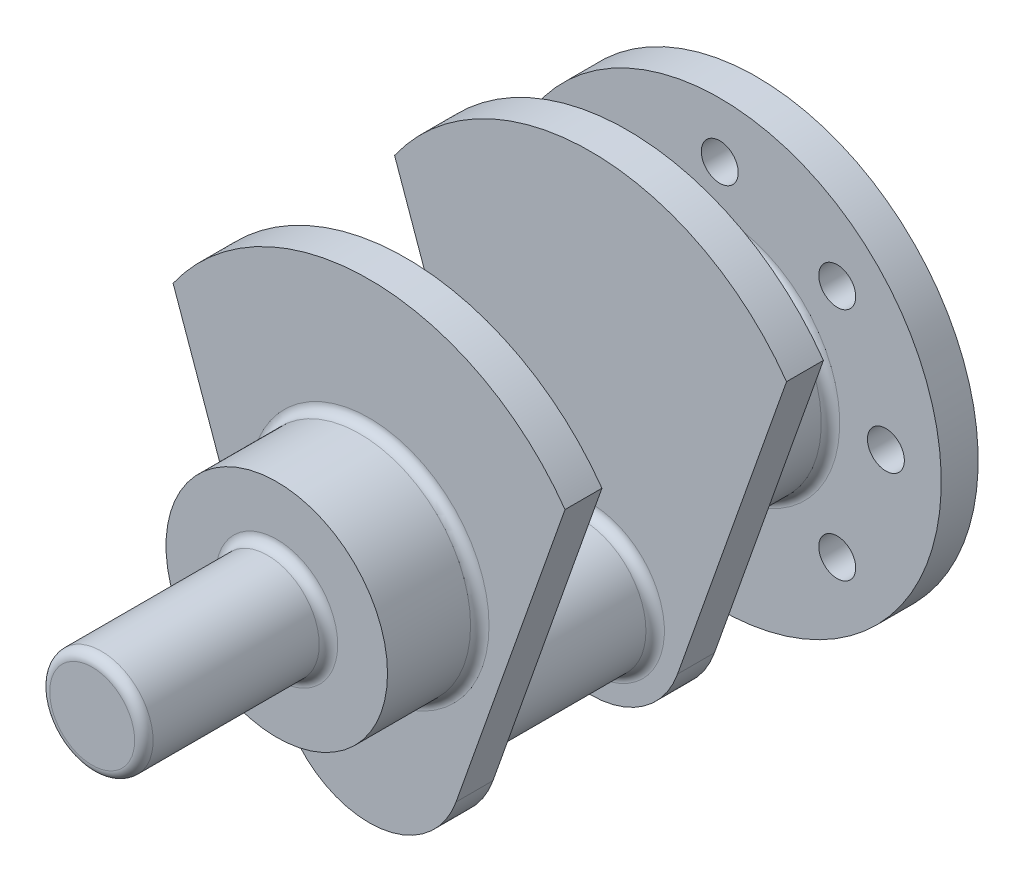
SolidWorks part; units mm, degrees
ref_plane "前视基准面" through (0, 0, 0) normal (0, 0, 1) x (1, 0, 0)
ref_plane "上视基准面" through (0, 0, 0) normal (0, 1, 0) x (1, 0, 0)
ref_plane "右视基准面" through (0, 0, 0) normal (1, 0, 0) x (0, 0, -1)
other "Configuration Table"
sketch "草图1" plane through (0, 0, 0) normal (0, 0, 1) x (1, 0, 0)
  line L0 (0, 60.1764) -> (0, -75) construction
  line L1 (-83.4577, 0) -> (70.0413, 0) construction
  line L2 (-106.1681, 75.0222) -> (-47.1321, -91.6903)
  line L3 (106.1681, 75.0222) -> (47.1321, -91.6903)
  circle A0 centre (0, -75) radius 50
  arc A1 (-106.1681, 75.0222) -> (106.1681, 75.0222) centre (0, 0) cw
  dimension "D1" = 100
  dimension "D3" = 130
  dimension "D2" = 39
  dimension "D4" = 75
extrude "凸台-拉伸1" add sketch "草图1" along normal blind 20 contours A1 L2 A0 L3 | A0
sketch "草图2" plane through (0, 0, 0) normal (0, 0, -1) x (-1, 0, 0)
  circle A0 centre (0, -75) radius 35
extrude "凸台-拉伸2" add sketch "草图2" along normal blind 100
sketch "草图3" plane through (0, 0, 20) normal (0, 0, 1) x (1, 0, 0)
  circle A0 centre (0, 0) radius 60
  dimension "D1" = 120
extrude "凸台-拉伸3" add sketch "草图3" along normal blind 50
ref_plane "基准面1" through (0, 0, -50) normal (0, 0, -1) x (-1, 0, 0)
mirror "镜向1" about plane through (0, 0, -50) normal (0, 0, -1) of "凸台-拉伸1", "凸台-拉伸3"
sketch "草图5" plane through (0, 0, 70) normal (0, 0, 1) x (1, 0, 0)
  circle A0 centre (0, 0) radius 28
extrude "凸台-拉伸4" add sketch "草图5" along normal blind 100
sketch "草图7" plane through (0, 0, -170) normal (0, 0, -1) x (-1, 0, 0)
  circle A0 centre (0, 0) radius 90 construction
  circle A1 centre (0, 0) radius 120
  circle A2 centre (0, 90) radius 10
  circle A3 centre (63.6396, 63.6396) radius 10
  circle A4 centre (90, 0) radius 10
  circle A5 centre (63.6396, -63.6396) radius 10
  circle A6 centre (0, -90) radius 10
  circle A7 centre (-63.6396, -63.6396) radius 10
  circle A8 centre (-90, 0) radius 10
  circle A9 centre (-63.6396, 63.6396) radius 10
  circle A10 centre (0, 0) radius 60 construction
  point P22 (0, 0)
  dimension "D1" = 8
  dimension "D2" = 20
  dimension "D5" = 180
  dimension "D6" = 240
extrude "凸台-拉伸5" add sketch "草图7" along normal blind 20
fillet "圆角1" radius 5 7 edges at (60, 0, -170) (60, 0, -120) (-35, -75, -100) (35, -75, 0) (60, 0, 20) (28, 0, 70) (28, 0, 170)
